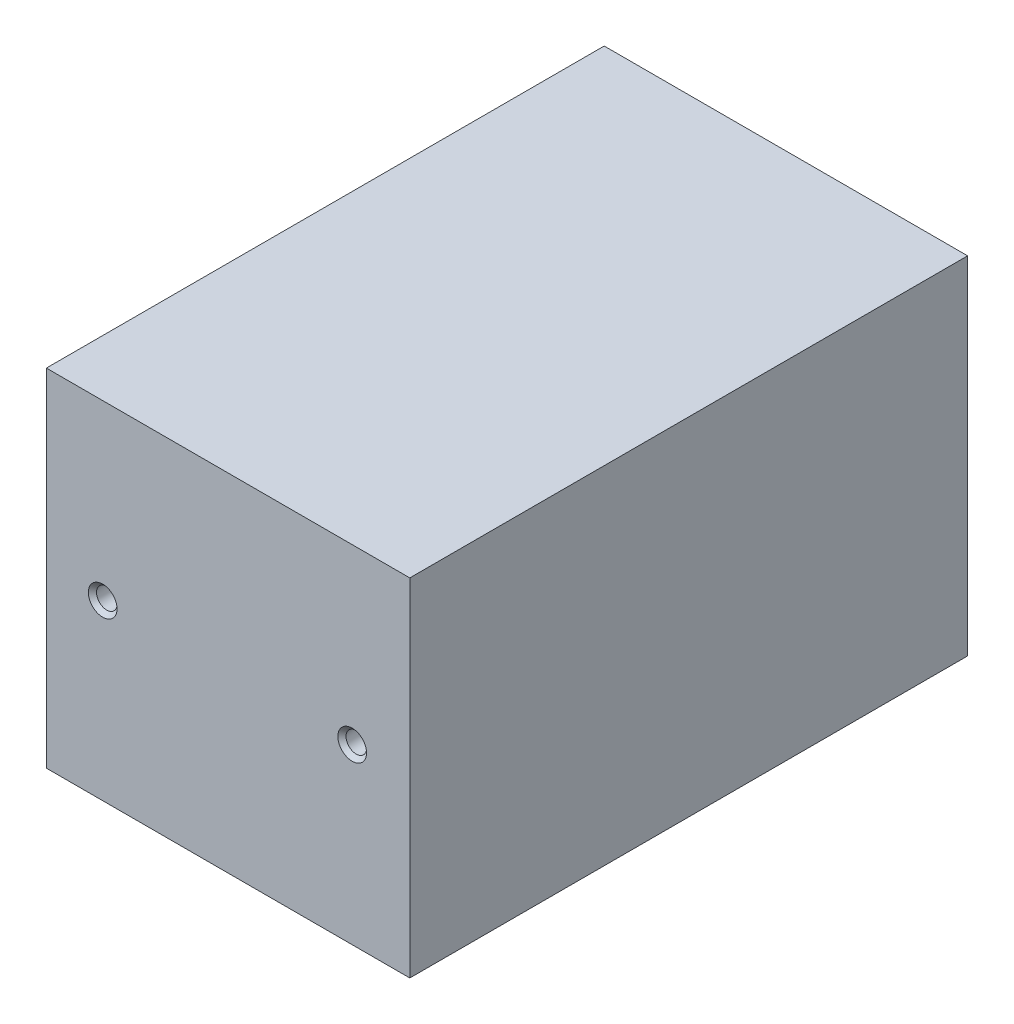
SolidWorks part; units mm, degrees
ref_plane "Front Plane" through (0, 0, 0) normal (0, 0, 1) x (1, 0, 0)
ref_plane "Top Plane" through (0, 0, 0) normal (0, 1, 0) x (1, 0, 0)
ref_plane "Right Plane" through (0, 0, 0) normal (1, 0, 0) x (0, 0, -1)
sketch "Sketch4" plane through (0, 0, 0) normal (0, 1, 0) x (1, 0, 0)
  line L1 (-44.3132, -65.2678) -> (44.3132, -65.2678)
  line L2 (-44.3132, -65.2678) -> (-44.3132, 65.2678)
  line L3 (-44.3132, 65.2678) -> (44.3132, 65.2678)
  line L4 (44.3132, -65.2678) -> (44.3132, 65.2678)
  line L5 (-44.3132, -65.2678) -> (44.3132, 65.2678) construction
  line L6 (-44.3132, 65.2678) -> (44.3132, -65.2678) construction
  circle A0 centre (-10.0348, 52.4178) radius 10.85 construction
  circle A1 centre (31.4632, 6.3529) radius 10.85 construction
  point P0 (0, 0)
  dimension "D1" = 2
  dimension "D2" = 2
extrude "Boss-Extrude3" add sketch "Sketch4" along normal mid plane 84.5
shell "Shell1" thickness 1
sketch "Sketch5" plane through (0, 0, 65.2678) normal (0, 0, 1) x (1, 0, 0)
  line L1 (-44.3132, -42.25) -> (44.3132, -42.25)
  line L2 (-44.3132, -42.25) -> (-44.3132, 42.25)
  line L3 (-44.3132, 42.25) -> (44.3132, 42.25)
  line L4 (44.3132, -42.25) -> (44.3132, 42.25)
extrude "Boss-Extrude4" add sketch "Sketch5" along normal blind 5.5
sketch "Sketch6" plane through (0, 0, 70.7678) normal (0, 0, 1) x (1, 0, 0)
  line L0 (-51.1669, 0) -> (50.5596, 0) construction
  circle A4 centre (-30.5781, 0) radius 3
  circle A5 centre (30.266, 0) radius 3
  point P18 (-30.5781, 0)
  point P21 (30.266, 0)
  dimension "D1" = 6
  dimension "D2" = 6
hole_wizard "M6x1.0 Tapped Hole1" positions "Sketch6" profile "Sketch7" tap size "M6x1.0" standard "ANSI Metric" end condition up to next
sketch "Sketch7" plane through (30.266, 0, 70.7678) normal (1, 0, 0) x (0, -1, 0)
  line L0 (0, 0) -> (0, 6.5)
  line L1 (0, 6.5) -> (2.5, 6.5)
  line L2 (2.5, 6.5) -> (2.5, 1)
  line L3 (2.5, 1) -> (3.5, 0)
  line L5 (3.5, 0) -> (0, 0)
  line L6 (-2.5, 1) -> (-3.5, 0) construction
  line L11 (0, -6.35) -> (0, 107.95) construction
  dimension "Thru Tap Drill Dia." = 5
  dimension "Thru Tap Drill Depth" = 6.5
  dimension "Near C'Sink Dia." = 7
  dimension "Near C'Sink Angle" = 90
